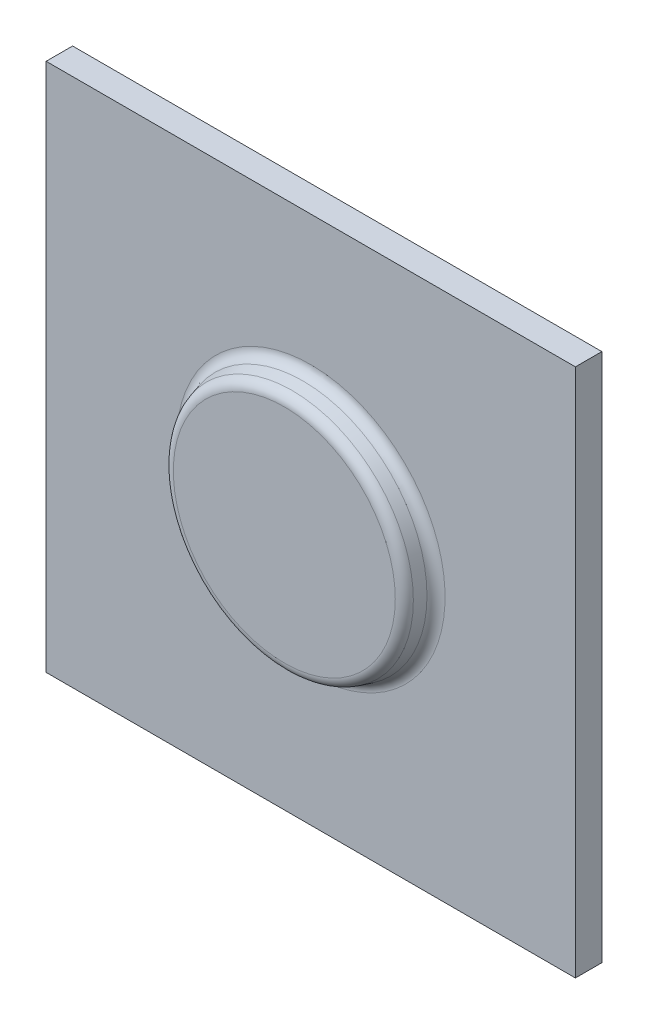
SolidWorks part; units mm, degrees
ref_plane "前视基准面" through (0, 0, 0) normal (0, 0, 1) x (1, 0, 0)
ref_plane "上视基准面" through (0, 0, 0) normal (0, 1, 0) x (1, 0, 0)
ref_plane "右视基准面" through (0, 0, 0) normal (1, 0, 0) x (0, 0, -1)
sketch "草图1" plane through (0, 0, 0) normal (0, 0, 1) x (1, 0, 0)
  line L1 (50, 50) -> (-50, 50)
  line L2 (50, 50) -> (50, -50)
  line L3 (50, -50) -> (-50, -50)
  line L4 (-50, 50) -> (-50, -50)
  line L5 (50, 50) -> (-50, -50) construction
  line L6 (50, -50) -> (-50, 50) construction
  point P0 (0, 0)
  dimension "D1" = 100
  dimension "D2" = 100
extrude "凸台-拉伸1" add sketch "草图1" along normal blind 5
sketch "草图2" plane through (0, 0, 5) normal (0, 0, 1) x (1, 0, 0)
  circle A0 centre (0, 0) radius 22.5
  dimension "D1" = 45
extrude "凸台-拉伸2" add sketch "草图2" along normal blind 5
draft "拔模1" type of draft neutral plane draft angle 15 faces to draft 1 face at (22.5, 0, 10) neutral plane through (0, 0, 10) neutral plane normal (0, 0, 1) parameters "D1"=15
fillet "圆角1" radius 2 2 edges at (-23.8397, 0, 5) (22.5, 0, 10)
sketch "方向草图" plane through (0, 0, 5) normal (0, 0, 1) x (1, 0, 0)
  line L0 (-50, 50) -> (-50, -50) construction
  line L1 (-50, -50) -> (50, -50) construction
  line L2 (50, -50) -> (50, 50) construction
  line L3 (50, 50) -> (-50, 50) construction
  line L4 (-50, 50) -> (-50, -50) construction
  line L5 (-50, -50) -> (50, -50) construction
  line L6 (50, -50) -> (50, 50) construction
  line L7 (50, 50) -> (-50, 50) construction
  circle A0 centre (0, 0) radius 25.3744 construction
  circle A1 centre (0, 0) radius 25.3744
  point P7 (0, 0)
other "成形工具1"
